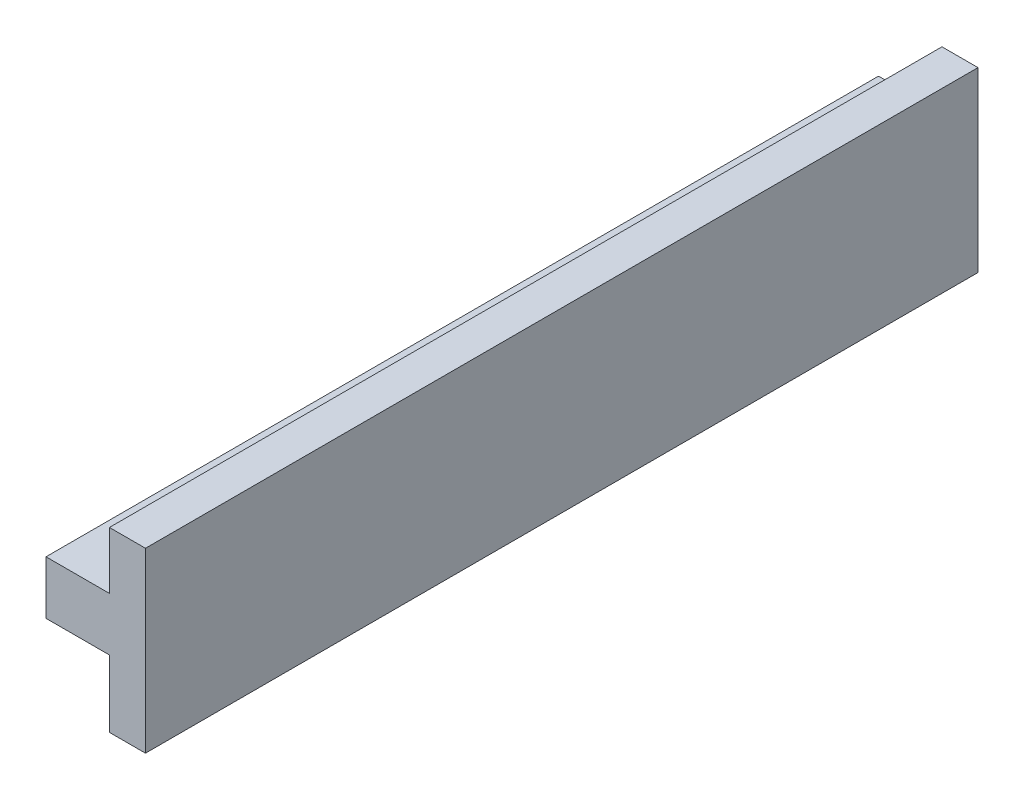
SolidWorks part; units mm, degrees
ref_plane "Front Plane" through (0, 0, 0) normal (0, 0, 1) x (1, 0, 0)
ref_plane "Top Plane" through (0, 0, 0) normal (0, 1, 0) x (1, 0, 0)
ref_plane "Right Plane" through (0, 0, 0) normal (1, 0, 0) x (0, 0, -1)
sketch "Sketch1" plane through (0, 0, -35.1738) normal (0, 0, 1) x (1, 0, 0)
  line L0 (79.4986, 40.052) -> (106.5851, 40.052) construction
  line L1 (85.9614, 43.752) -> (94.7614, 43.752)
  line L2 (94.7614, 36.352) -> (85.9614, 36.352)
  line L3 (85.9614, 36.352) -> (85.9614, 43.752)
  line L4 (94.7614, 51.6762) -> (94.7614, 27.052) construction
  line L5 (99.7614, 51.6762) -> (99.7614, 27.052)
  line L6 (99.7614, 51.6762) -> (94.7614, 51.6762)
  line L7 (94.7614, 51.6762) -> (94.7614, 43.752)
  line L8 (99.7614, 27.052) -> (94.7614, 27.052)
  line L9 (94.7614, 27.052) -> (94.7614, 36.352)
  dimension "D1" = 5
ref_plane "Plane3" through (0, 0, -41.2738) normal (0, 0, 1) x (1, 0, 0)
sketch "Sketch4" plane through (0, 0, -41.2738) normal (0, 0, 1) x (1, 0, 0)
  line L0 (99.7614, 51.6762) -> (99.7614, 27.052) construction
  line L1 (99.7614, 51.6762) -> (94.7614, 51.6762) construction
  line L2 (94.7614, 51.6762) -> (94.7614, 43.752) construction
  line L3 (85.9614, 43.752) -> (94.7614, 43.752) construction
  line L4 (85.9614, 36.352) -> (85.9614, 43.752) construction
  line L5 (94.7614, 36.352) -> (85.9614, 36.352) construction
  line L6 (94.7614, 27.052) -> (94.7614, 36.352) construction
  line L7 (99.7614, 27.052) -> (94.7614, 27.052) construction
  line L8 (99.7614, 51.6762) -> (99.7614, 27.052)
  line L9 (99.7614, 51.6762) -> (94.7614, 51.6762)
  line L10 (94.7614, 51.6762) -> (94.7614, 43.752)
  line L11 (85.9614, 43.752) -> (94.7614, 43.752)
  line L12 (85.9614, 36.352) -> (85.9614, 43.752)
  line L13 (94.7614, 36.352) -> (85.9614, 36.352)
  line L14 (94.7614, 27.052) -> (94.7614, 36.352)
  line L15 (99.7614, 27.052) -> (94.7614, 27.052)
extrude "Extrude2" add sketch "Sketch1" against normal blind 115.5
